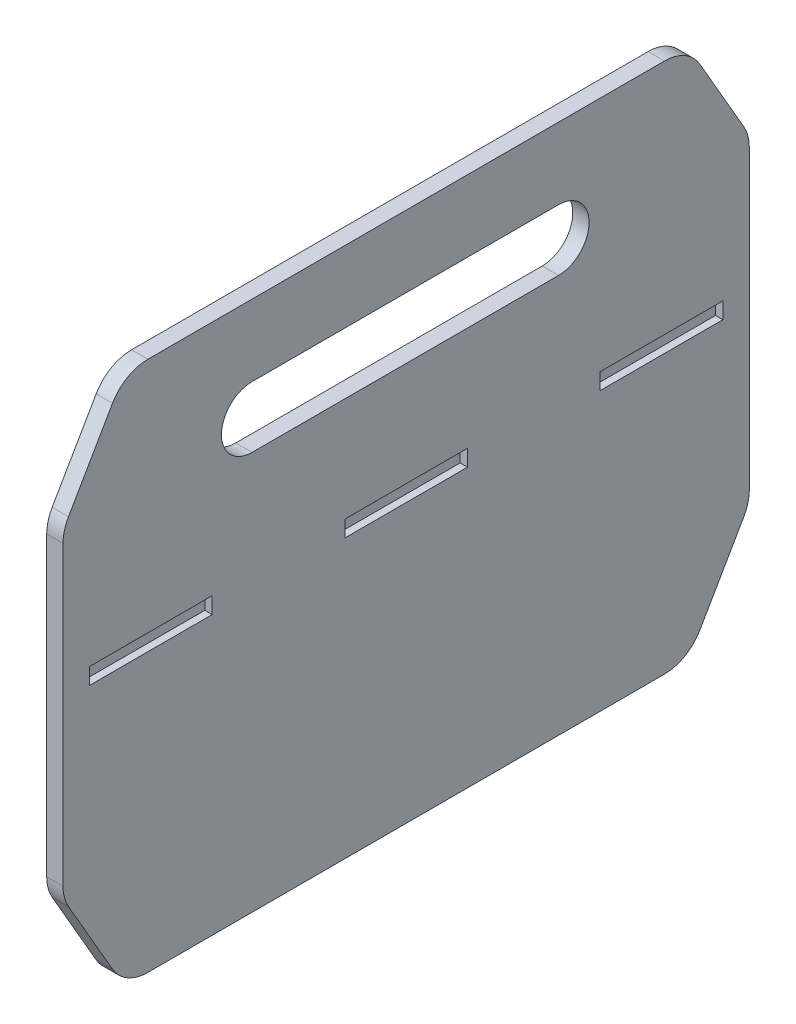
SolidWorks part; units mm, degrees
ref_plane "Front Plane" through (0, 0, 0) normal (0, 0, 1) x (1, 0, 0)
ref_plane "Top Plane" through (0, 0, 0) normal (0, 1, 0) x (1, 0, 0)
ref_plane "Right Plane" through (0, 0, 0) normal (1, 0, 0) x (0, 0, -1)
sketch "Sketch1" plane through (0, 0, 0) normal (1, 0, 0) x (0, 0, -1)
  line L0 (0, 254) -> (0, 0) construction
  line L2 (-212.8026, 0) -> (-212.8026, 254)
  line L4 (213.9174, 0) -> (213.9174, 254)
  line L5 (-95.25, 215.9) -> (95.25, 215.9) construction
  line L6 (-95.25, 234.95) -> (95.25, 234.95)
  line L7 (-95.25, 196.85) -> (95.25, 196.85)
  line L8 (-212.8026, 127) -> (213.9174, 127) construction
  line L10 (-212.8026, 169.926) -> (-212.8026, 160.274) construction
  line L13 (-212.8026, 0) -> (213.9174, 0) construction
  line L15 (-212.8026, 254) -> (-212.8026, 279.4)
  line L16 (-212.8026, 279.4) -> (213.9174, 279.4)
  line L17 (213.36, 195.326) -> (213.9174, 166.37) construction
  line L18 (213.9174, 254) -> (213.9174, 279.4)
  line L20 (-212.8026, 0) -> (-212.8026, -50.8)
  line L36 (-212.8026, -50.8) -> (213.9174, -50.8)
  line L37 (213.9174, 0) -> (213.9174, -50.8)
  line L39 (213.9174, 254) -> (-212.8026, 254) construction
  line L40 (-212.8026, 12.7) -> (213.9174, 12.7) construction
  arc A0 (-95.25, 234.95) -> (-95.25, 196.85) centre (-95.25, 215.9) ccw
  arc A1 (95.25, 196.85) -> (95.25, 234.95) centre (95.25, 215.9) ccw
  point P10 (0, 215.9)
  point P54 (0.5574, 127)
  dimension "D1" = 254
  dimension "D2" = 426.72
  dimension "D3" = 190.5
  dimension "D4" = 19.05
  dimension "D5" = 38.1
  dimension "D7" = 25.4
  dimension "1" = 50.8
extrude "Boss-Extrude1" add sketch "Sketch1" against normal blind 10.16
sketch "Sketch2" plane through (0, 0, 0) normal (1, 0, 0) x (0, 0, -1)
  line L14 (-212.8026, 127) -> (213.9174, 127) construction
  line L15 (-196.2926, 132.08) -> (-120.0926, 132.08)
  line L16 (-196.2926, 132.08) -> (-196.2926, 121.92)
  line L17 (-196.2926, 121.92) -> (-120.0926, 121.92)
  line L18 (-120.0926, 132.08) -> (-120.0926, 121.92)
  line L19 (-212.8026, 0) -> (-212.8026, 254) construction
  line L20 (-37.5426, 132.08) -> (38.6574, 132.08)
  line L21 (-37.5426, 132.08) -> (-37.5426, 121.92)
  line L22 (38.6574, 132.08) -> (38.6574, 121.92)
  line L23 (-37.5426, 121.92) -> (38.6574, 121.92)
  line L24 (121.2074, 132.08) -> (197.4074, 132.08)
  line L25 (121.2074, 132.08) -> (121.2074, 121.92)
  line L26 (197.4074, 132.08) -> (197.4074, 121.92)
  line L27 (121.2074, 121.92) -> (197.4074, 121.92)
  point P6 (-196.2926, 127)
  dimension "D1" = 16.51
  dimension "D2" = 10.16
  dimension "D3" = 76.2
  dimension "D4" = 3
extrude "Cut-Extrude1" cut sketch "Sketch2" against normal blind 4.572
chamfer "Chamfer1" distance 38.1 angle 60 4 edges at (-5.08, -50.8, -213.9174) (-5.08, 279.4, 212.8026) (-5.08, -50.8, 212.8026) (-5.08, 279.4, -213.9174)
fillet "Fillet1" radius 25.4 8 edges at (-5.08, 279.4, 174.7026) (-5.08, 213.4089, 212.8026) (-5.08, 15.1911, 212.8026) (-5.08, -50.8, 174.7026) (-5.08, -50.8, -175.8174) (-5.08, 15.1911, -213.9174) (-5.08, 213.4089, -213.9174) (-5.08, 279.4, -175.8174)
sketch "Sketch5" plane through (-10.16, 0, 0) normal (-1, 0, 0) x (0, 0, 1)
  line L0 (-138.2945, 154.178) -> (138.2945, 154.178) construction
  line L3 (212.8026, 127) -> (-213.9174, 127) construction
  line L5 (-187.96, 154.178) -> (-187.96, 166.878) construction
  line L6 (0, 181.356) -> (0, 127) construction
  line L7 (0, 254) -> (0, 0) construction
  line L8 (-205.74, 127) -> (205.74, 127) construction
  point P8 (-198.882, 154.178)
  point P9 (-177.038, 154.178)
  point P14 (187.96, 166.878)
  point P18 (0, 154.178)
  point P19 (177.038, 154.178)
  point P20 (198.882, 154.178)
  point P21 (198.882, 99.822)
  point P26 (0, 127)
  point P27 (177.038, 99.822)
  point P28 (187.96, 87.122)
  point P29 (-177.038, 99.822)
  point P30 (-198.882, 99.822)
  point P31 (-187.96, 87.122)
  dimension "D1" = 27.178
  dimension "D3" = 21.844
  dimension "D4" = 10.922
  dimension "D5" = 12.7
sketch "Sketch7" plane through (-10.16, 0, 0) normal (-1, 0, 0) x (0, 0, 1)
  point P0 (-198.882, 154.178)
  point P3 (-187.96, 166.878)
  point P6 (-177.038, 154.178)
  point P9 (198.882, 154.178)
  point P12 (177.038, 154.178)
  point P15 (187.96, 166.878)
  point P19 (-177.038, 99.822)
  point P22 (-187.96, 87.122)
  point P25 (-198.882, 99.822)
  point P28 (177.038, 99.822)
  point P31 (187.96, 87.122)
  point P34 (198.882, 99.822)
hole_wizard "CBORE for #3 Socket Head Cap Screw1" positions "Sketch7" profile "Sketch8" counterbore size "#3" standard "ANSI Inch"
sketch "Sketch8" plane through (-10.16, 154.178, -198.882) normal (0, 1, 0) x (0, 0, 1)
  line L0 (0, 0) -> (0, 10.16)
  line L1 (0, 10.16) -> (1.524, 10.16)
  line L3 (1.524, 10.16) -> (1.524, 2.5146)
  line L4 (1.524, 2.5146) -> (2.5794, 2.5146)
  line L5 (2.5794, 2.5146) -> (2.5794, 0)
  line L7 (2.5794, 0) -> (0, 0)
  line L11 (0, -6.35) -> (0, 107.95) construction
  dimension "Thru Hole Dia." = 3.048
  dimension "Thru Hole Depth" = 10.16
  dimension "C'Bore Dia." = 5.1587
  dimension "C'Bore Depth" = 2.5146
sketch "Sketch9" plane through (0, 0, 0) normal (1, 0, 0) x (0, 0, -1)
  line L0 (114.3, 215.9) -> (205.74, 215.9) construction
  line L1 (205.74, 1.9929) -> (205.74, 226.6071) construction
  arc A0 (95.25, 196.85) -> (95.25, 234.95) centre (95.25, 215.9) ccw construction
  point P7 (160.02, 215.9)
sketch "Sketch10" plane through (-10.16, 0, 0) normal (-1, 0, 0) x (0, 0, 1)
  line L0 (196.2926, 121.92) -> (120.0926, 121.92) construction
  line L1 (149.8806, 121.92) -> (213.3806, 121.92) construction
  line L2 (149.8806, 121.92) -> (149.8806, 20.32) construction
  line L3 (149.8806, 20.32) -> (213.3806, 20.32) construction
  line L4 (213.3806, 121.92) -> (213.3806, 20.32) construction
  line L7 (137.1806, 121.92) -> (117.4936, 121.92) construction
  line L8 (137.1806, 121.92) -> (137.1806, 103.126) construction
  line L9 (137.1806, 103.126) -> (117.4936, 103.126) construction
  line L10 (117.4936, 121.92) -> (117.4936, 103.126) construction
  dimension "D1" = 12.7
  dimension "D2" = 101.6
  dimension "D3" = 63.5
equation "\"D4@Sketch5\"=\"D3@Sketch5\"/2"
